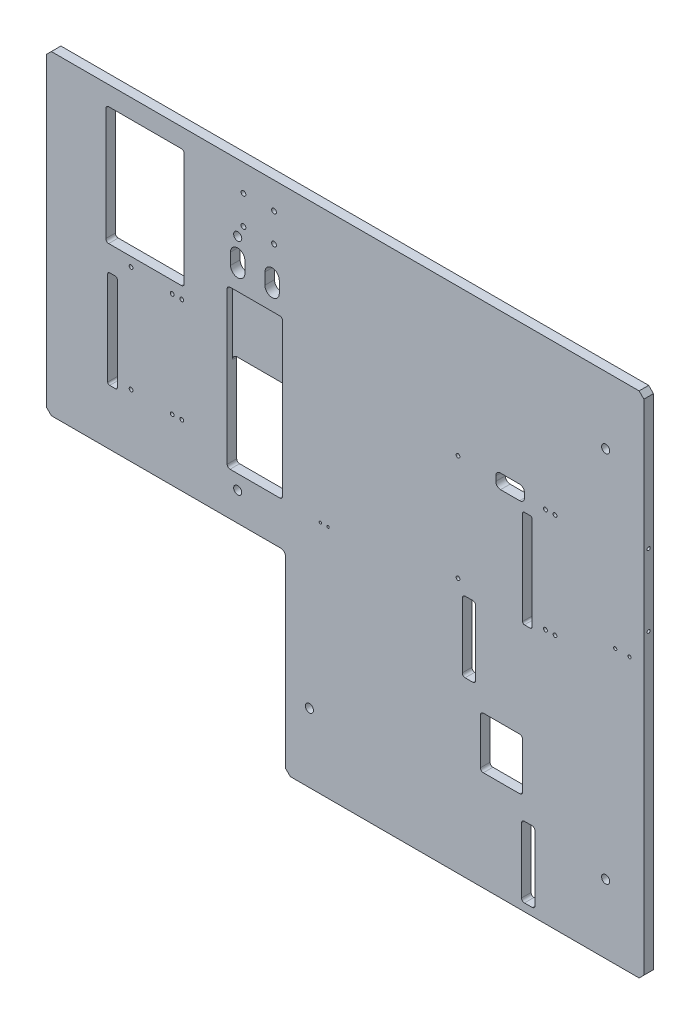
SolidWorks part; units mm, degrees
ref_plane "Front Plane" through (0, 0, 0) normal (0, 0, 1) x (1, 0, 0)
ref_plane "Top Plane" through (0, 0, 0) normal (0, 1, 0) x (1, 0, 0)
ref_plane "Right Plane" through (0, 0, 0) normal (1, 0, 0) x (0, 0, -1)
sketch "Sketch1" plane through (0, 0, 0) normal (0, 0, 1) x (1, 0, 0)
  line L1 (-81.7319, 190.6221) -> (543.2681, 190.6221)
  line L2 (-81.7319, 190.6221) -> (-81.7319, -139.3779)
  line L3 (-81.7319, -139.3779) -> (168.2681, -139.3779)
  line L4 (543.2681, 190.6221) -> (543.2681, -341.3779)
  line L5 (-19.7319, 170.6221) -> (62.2681, 170.6221)
  line L6 (372.2681, -182.8779) -> (416.2681, -182.8779)
  line L7 (543.2681, -341.3779) -> (168.2681, -341.3779)
  line L8 (168.2681, -139.3779) -> (168.2681, -341.3779)
  line L9 (-19.7319, 170.6221) -> (-19.7319, 46.6221)
  line L10 (-19.7319, 46.6221) -> (62.2681, 46.6221)
  line L11 (62.2681, 170.6221) -> (62.2681, 46.6221)
  line L12 (-17.7319, 20.6221) -> (-7.7319, 20.6221)
  line L13 (-17.7319, 20.6221) -> (-17.7319, -81.3779)
  line L14 (-17.7319, -81.3779) -> (-7.7319, -81.3779)
  line L15 (-7.7319, 20.6221) -> (-7.7319, -81.3779)
  line L16 (372.2681, -182.8779) -> (372.2681, -236.8779)
  line L17 (110.7681, 102.6221) -> (110.7681, 90.6221)
  line L18 (372.2681, -236.8779) -> (416.2681, -236.8779)
  line L19 (125.7681, 102.6221) -> (125.7681, 90.6221)
  line L20 (416.2681, -182.8779) -> (416.2681, -236.8779)
  line L21 (146.7681, 102.6221) -> (146.7681, 90.6221)
  line L22 (353.2681, -86.3779) -> (367.2681, -86.3779)
  line L23 (161.7681, 102.6221) -> (161.7681, 90.6221)
  line L24 (415.2681, -259.3779) -> (429.2681, -259.3779)
  line L25 (415.2681, -259.3779) -> (415.2681, -333.3779)
  line L26 (415.2681, -333.3779) -> (429.2681, -333.3779)
  line L27 (429.2681, -259.3779) -> (429.2681, -333.3779)
  line L28 (353.2681, -86.3779) -> (353.2681, -160.3779)
  line L29 (353.2681, -160.3779) -> (367.2681, -160.3779)
  line L30 (367.2681, -86.3779) -> (367.2681, -160.3779)
  line L31 (388.2681, 43.6221) -> (418.2681, 43.6221)
  line L32 (388.2681, 43.6221) -> (388.2681, 28.6221)
  line L33 (388.2681, 28.6221) -> (418.2681, 28.6221)
  line L34 (418.2681, 43.6221) -> (418.2681, 28.6221)
  line L35 (416.2681, 20.6221) -> (426.2681, 20.6221)
  line L36 (416.2681, 20.6221) -> (416.2681, -81.3779)
  line L37 (416.2681, -81.3779) -> (426.2681, -81.3779)
  line L38 (426.2681, 20.6221) -> (426.2681, -81.3779)
  arc A0 (125.7681, 102.6221) -> (110.7681, 102.6221) centre (118.2681, 102.6221) ccw
  arc A1 (110.7681, 90.6221) -> (125.7681, 90.6221) centre (118.2681, 90.6221) ccw
  arc A2 (146.7681, 90.6221) -> (161.7681, 90.6221) centre (154.2681, 90.6221) ccw
  arc A5 (161.7681, 102.6221) -> (146.7681, 102.6221) centre (154.2681, 102.6221) ccw
  dimension "D1" = 625
  dimension "D2" = 330
  dimension "D3" = 250
  dimension "D4" = 144
  dimension "D5" = 62
  dimension "D6" = 20
  dimension "D7" = 144
  dimension "D8" = 170
  dimension "D9" = 272
  dimension "D10" = 64
  dimension "D11" = 74
  dimension "D12" = 15
  dimension "D13" = 15
  dimension "D14" = 532
  dimension "D15" = 450
  dimension "D16" = 524
  dimension "D17" = 497
  dimension "D18" = 511
  dimension "D19" = 373.5
  dimension "D20" = 427.5
  dimension "D21" = 454
  dimension "D22" = 498
  dimension "D23" = 277
  dimension "D24" = 351
  dimension "D25" = 435
  dimension "D26" = 449
  dimension "D27" = 470
  dimension "D28" = 30
  dimension "D29" = 147
  dimension "D30" = 162
  dimension "D31" = 170
  dimension "D32" = 272
  dimension "D33" = 508
  dimension "D34" = 498
  dimension "D35" = 200
  dimension "D36" = 236
  dimension "D37" = 88
  dimension "D38" = 100
  dimension "D39" = 12
extrude "Boss-Extrude1" add sketch "Sketch1" along normal blind 10
fillet "Fillet1" radius 3 4 edges at (-19.7319, 46.6221, 5) (62.2681, 46.6221, 5) (62.2681, 170.6221, 5) (-19.7319, 170.6221, 5)
fillet "Fillet2" radius 2 4 edges at (-17.7319, -81.3779, 5) (-7.7319, -81.3779, 5) (-7.7319, 20.6221, 5) (-17.7319, 20.6221, 5)
fillet "Fillet3" radius 5 4 edges at (388.2681, 28.6221, 5) (418.2681, 28.6221, 5) (418.2681, 43.6221, 5) (388.2681, 43.6221, 5)
fillet "Fillet4" radius 2 4 edges at (426.2681, -81.3779, 5) (416.2681, -81.3779, 5) (426.2681, 20.6221, 5) (416.2681, 20.6221, 5)
fillet "Fillet5" radius 3 12 edges at (429.2681, -333.3779, 5) (415.2681, -333.3779, 5) (429.2681, -259.3779, 5) (415.2681, -259.3779, 5) (416.2681, -236.8779, 5) (416.2681, -182.8779, 5) (372.2681, -182.8779, 5) (372.2681, -236.8779, 5) (367.2681, -160.3779, 5) (353.2681, -160.3779, 5) (367.2681, -86.3779, 5) (353.2681, -86.3779, 5)
chamfer "Chamfer1" distance 5 angle 45 5 edges at (543.2681, 190.6221, 5) (543.2681, -341.3779, 5) (168.2681, -341.3779, 5) (-81.7319, -139.3779, 5) (-81.7319, 190.6221, 5)
fillet "Fillet6" radius 5 1 edges at (168.2681, -139.3779, 5)
sketch "Sketch2" plane through (0, 0, 10) normal (0, 0, 1) x (1, 0, 0)
  line L0 (538.2681, 190.6221) -> (-76.7319, 190.6221) construction
  line L1 (107.2681, 70.6221) -> (165.2681, 70.6221)
  line L2 (107.2681, 70.6221) -> (107.2681, -94.3779)
  line L3 (107.2681, -94.3779) -> (165.2681, -94.3779)
  line L4 (165.2681, 70.6221) -> (165.2681, -94.3779)
  line L6 (-81.7319, 185.6221) -> (-81.7319, -134.3779) construction
  dimension "D1" = 120
  dimension "D2" = 285
  dimension "D3" = 189
  dimension "D4" = 247
extrude "Cut-Extrude1" cut sketch "Sketch2" against normal blind 5.5
sketch "Sketch3" plane through (0, 0, 4.5) normal (0, 0, 1) x (1, 0, 0)
  line L0 (107.2681, 70.6221) -> (107.2681, -94.3779) construction
  line L1 (165.2681, -94.3779) -> (107.2681, -94.3779)
  line L2 (165.2681, -94.3779) -> (165.2681, 5.6221)
  line L3 (165.2681, 5.6221) -> (107.2681, 5.6221)
  line L4 (107.2681, -94.3779) -> (107.2681, 5.6221)
  dimension "D1" = 100
extrude "Cut-Extrude2" cut sketch "Sketch3" against normal through all
fillet "Fillet7" radius 3 4 edges at (107.2681, -94.3779, 5) (165.2681, -94.3779, 5) (165.2681, 70.6221, 7.25) (107.2681, 70.6221, 7.25)
fillet "Fillet8" radius 5 2 edges at (165.2681, 5.6221, 2.25) (107.2681, 5.6221, 2.25)
sketch "Sketch4" plane through (0, 0, 10) normal (0, 0, 1) x (1, 0, 0)
  line L0 (538.2681, 190.6221) -> (-76.7319, 190.6221) construction
  line L1 (-81.7319, 185.6221) -> (-81.7319, -134.3779) construction
  circle A0 centre (6.7681, 37.1221) radius 2
  circle A1 centre (6.7681, -73.8779) radius 2
  circle A2 centre (348.7681, 37.1221) radius 2
  circle A3 centre (348.7681, -73.8779) radius 2
  dimension "D2" = 4
  dimension "D1" = 153.5
  dimension "D3" = 264.5
  dimension "D4" = 88.5
  dimension "D5" = 430.5
extrude "Cut-Extrude3" cut sketch "Sketch4" against normal through all
hole_wizard "M4 Tapped Hole1" positions "Sketch5" profile "Sketch6" tap size "M4" standard "ISO"
sketch "Sketch5" plane through (-81.7319, 0, 0) normal (-1, 0, 0) x (0, 0, 1)
  line L0 (0, 185.6221) -> (0, -134.3779) construction
  line L1 (0, 190.6221) -> (10, 190.6221) construction
  point P0 (5, 47.6221)
  point P2 (5, -27.3779)
  dimension "D1" = 5
  dimension "D2" = 143
  dimension "D3" = 218
sketch "Sketch6" plane through (-81.7319, 47.6221, 5) normal (0, 1, 0) x (0, 0, 1)
  line L0 (0, 0) -> (0, 8.9914)
  line L1 (0, 8.9914) -> (1.65, 8)
  line L2 (1.65, 8) -> (1.65, 0)
  line L5 (1.65, 0) -> (0, 0)
  line L10 (0, 8.9914) -> (-1.65, 8) construction
  line L11 (0, -6.35) -> (0, 107.95) construction
  dimension "Tap Drill Dia." = 3.3
  dimension "Tap Drill Depth" = 8
  dimension "Drill Angle" = 118
cosmetic thread "Hole Thread1" parameters "D1"=8, "D2"=4
cosmetic thread "Hole Thread2" parameters "D1"=8, "D2"=4
hole_wizard "M4 Tapped Hole2" positions "Sketch7" profile "Sketch8" tap size "M4" standard "ISO"
sketch "Sketch7" plane through (543.2681, 0, 0) normal (1, 0, 0) x (0, 0, -1)
  line L0 (0, 185.6221) -> (-10, 185.6221) construction
  line L1 (-10, 190.6221) -> (0, 190.6221) construction
  point P0 (-5, 47.6221)
  point P2 (-5, -27.3779)
  point P8 (-5, 185.6221)
  dimension "D1" = 143
  dimension "D2" = 218
sketch "Sketch8" plane through (543.2681, 47.6221, 5) normal (0, 1, 0) x (0, 0, -1)
  line L0 (0, 0) -> (0, 8.9914)
  line L1 (0, 8.9914) -> (1.65, 8)
  line L2 (1.65, 8) -> (1.65, 0)
  line L5 (1.65, 0) -> (0, 0)
  line L10 (0, 8.9914) -> (-1.65, 8) construction
  line L11 (0, -6.35) -> (0, 107.95) construction
  dimension "Tap Drill Dia." = 3.3
  dimension "Tap Drill Depth" = 8
  dimension "Drill Angle" = 118
cosmetic thread "Hole Thread3" parameters "D1"=8, "D2"=4
cosmetic thread "Hole Thread4" parameters "D1"=8, "D2"=4
hole_wizard "M10 Tapped Hole1" positions "Sketch9" profile "Sketch10" tap size "M10" standard "ISO" end condition through all
sketch "Sketch9" plane through (0, 0, 10) normal (0, 0, 1) x (1, 0, 0)
  line L0 (538.2681, 190.6221) -> (-76.7319, 190.6221) construction
  line L1 (-81.7319, 185.6221) -> (-81.7319, -134.3779) construction
  point P0 (118.2681, -109.3779)
  point P2 (193.2681, -269.3779)
  point P4 (503.2681, -269.3779)
  point P6 (118.2681, 120.6221)
  point P8 (503.2681, 120.6221)
  dimension "D1" = 70
  dimension "D2" = 200
  dimension "D3" = 300
  dimension "D4" = 460
  dimension "D5" = 275
  dimension "D6" = 585
sketch "Sketch10" plane through (118.2681, -109.3779, 10) normal (1, 0, 0) x (0, -1, 0)
  line L0 (0, 0) -> (0, 10)
  line L1 (0, 10) -> (4.25, 10)
  line L2 (4.25, 10) -> (4.25, 0)
  line L5 (4.25, 0) -> (0, 0)
  line L11 (0, -6.35) -> (0, 107.95) construction
  dimension "Thru Tap Drill Dia." = 8.5
  dimension "Thru Tap Drill Depth" = 10
cosmetic thread "Hole Thread5" parameters "D2"=10
cosmetic thread "Hole Thread6" parameters "D2"=10
cosmetic thread "Hole Thread7" parameters "D2"=10
cosmetic thread "Hole Thread8" parameters "D2"=10
cosmetic thread "Hole Thread9" parameters "D2"=10
hole_wizard "M4 Tapped Hole3" positions "Sketch12" profile "Sketch13" tap size "M4" standard "ISO"
sketch "Sketch12" plane through (0, 0, 10) normal (0, 0, 1) x (1, 0, 0)
  line L0 (538.2681, 190.6221) -> (-76.7319, 190.6221) construction
  line L1 (-81.7319, 185.6221) -> (-81.7319, -134.3779) construction
  point P0 (513.2681, -55.3779)
  point P2 (528.2681, -55.3779)
  dimension "D1" = 246
  dimension "D2" = 246
  dimension "D3" = 595
  dimension "D4" = 610
sketch "Sketch13" plane through (513.2681, -55.3779, 10) normal (1, 0, 0) x (0, -1, 0)
  line L0 (0, 0) -> (0, 11.0914)
  line L1 (0, 11.0914) -> (1.65, 10.1)
  line L2 (1.65, 10.1) -> (1.65, 0)
  line L5 (1.65, 0) -> (0, 0)
  line L10 (0, 11.0914) -> (-1.65, 10.1) construction
  line L11 (0, -6.35) -> (0, 107.95) construction
  dimension "Tap Drill Dia." = 3.3
  dimension "Tap Drill Depth" = 10.1
  dimension "Drill Angle" = 118
cosmetic thread "Hole Thread10" parameters "D1"=8, "D2"=4
cosmetic thread "Hole Thread11" parameters "D1"=8, "D2"=4
sketch "Sketch15" plane through (0, 0, 10) normal (0, 0, 1) x (1, 0, 0)
  line L0 (538.2681, 190.6221) -> (-76.7319, 190.6221) construction
  line L1 (-81.7319, 185.6221) -> (-81.7319, -134.3779) construction
  circle A0 centre (49.7681, 34.2221) radius 2
  circle A1 centre (49.7681, -74.7779) radius 2
  circle A2 centre (440.2681, 34.2221) radius 2
  circle A3 centre (440.2681, -74.7779) radius 2
  circle A4 centre (59.7681, 34.2221) radius 2
  circle A5 centre (59.7681, -74.7779) radius 2
  circle A6 centre (450.2681, 34.2221) radius 2
  circle A7 centre (450.2681, -74.7779) radius 2
  dimension "D1" = 4
  dimension "D2" = 156.4
  dimension "D3" = 265.4
  dimension "D4" = 131.5
  dimension "D5" = 522
  dimension "D6" = 10
  dimension "D7" = 10
extrude "Cut-Extrude4" cut sketch "Sketch15" against normal through all
hole_wizard "M3 Tapped Hole1" positions "Sketch17" profile "Sketch18" tap size "M3" standard "ISO"
sketch "Sketch17" plane through (0, 0, 10) normal (0, 0, 1) x (1, 0, 0)
  line L0 (-81.7319, 185.6221) -> (-81.7319, -134.3779) construction
  line L1 (538.2681, 190.6221) -> (-76.7319, 190.6221) construction
  point P0 (204.7681, -95.3779)
  point P2 (212.7681, -95.3779)
  dimension "D1" = 286.5
  dimension "D2" = 286
  dimension "D3" = 286
  dimension "D4" = 294.5
sketch "Sketch18" plane through (204.7681, -95.3779, 10) normal (1, 0, 0) x (0, -1, 0)
  line L0 (0, 0) -> (0, 8.2511)
  line L1 (0, 8.2511) -> (1.25, 7.5)
  line L2 (1.25, 7.5) -> (1.25, 0)
  line L5 (1.25, 0) -> (0, 0)
  line L10 (0, 8.2511) -> (-1.25, 7.5) construction
  line L11 (0, -6.35) -> (0, 107.95) construction
  dimension "Tap Drill Dia." = 2.5
  dimension "Tap Drill Depth" = 7.5
  dimension "Drill Angle" = 118
cosmetic thread "Hole Thread12" parameters "D1"=6, "D2"=3
cosmetic thread "Hole Thread13" parameters "D1"=6, "D2"=3
hole_wizard "M6 Tapped Hole1" positions "Sketch19" profile "Sketch20" tap size "M6" standard "ISO"
sketch "Sketch19" plane through (0, 0, 10) normal (0, 0, 1) x (1, 0, 0)
  line L0 (538.2681, 190.6221) -> (-76.7319, 190.6221) construction
  line L1 (-81.7319, 185.6221) -> (-81.7319, -134.3779) construction
  point P0 (124.2681, 162.6221)
  point P2 (156.2681, 162.6221)
  point P4 (124.2681, 132.6221)
  point P6 (156.2681, 132.6221)
  dimension "D1" = 28
  dimension "D2" = 58
  dimension "D3" = 238
  dimension "D4" = 206
sketch "Sketch20" plane through (124.2681, 162.6221, 10) normal (1, 0, 0) x (0, -1, 0)
  line L0 (0, 0) -> (0, 16.5022)
  line L1 (0, 16.5022) -> (2.5, 15)
  line L2 (2.5, 15) -> (2.5, 0)
  line L5 (2.5, 0) -> (0, 0)
  line L10 (0, 16.5022) -> (-2.5, 15) construction
  line L11 (0, -6.35) -> (0, 107.95) construction
  dimension "Tap Drill Dia." = 5
  dimension "Tap Drill Depth" = 15
  dimension "Drill Angle" = 118
cosmetic thread "Hole Thread14" parameters "D1"=10, "D2"=6
cosmetic thread "Hole Thread15" parameters "D1"=10, "D2"=6
cosmetic thread "Hole Thread16" parameters "D1"=10, "D2"=6
cosmetic thread "Hole Thread17" parameters "D1"=10, "D2"=6
